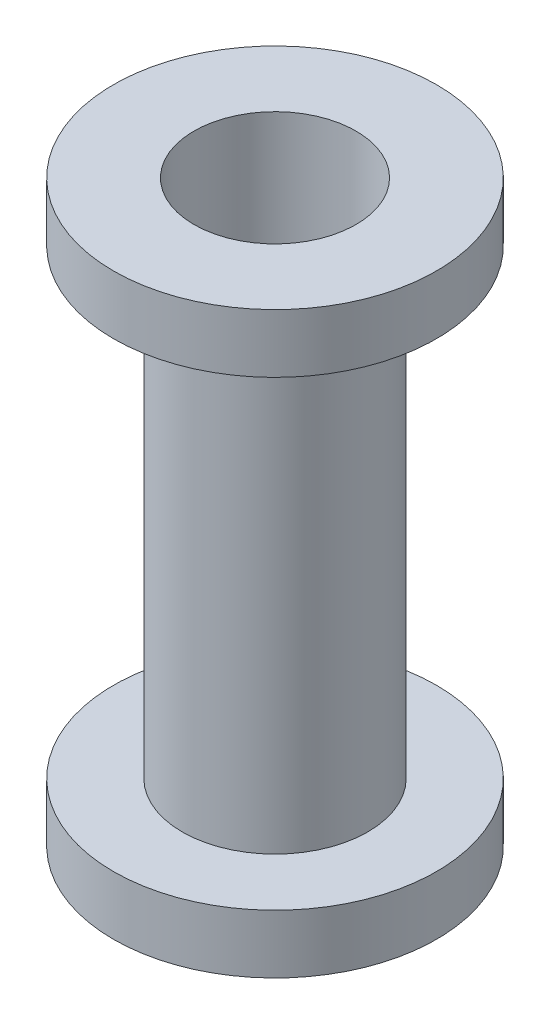
SolidWorks part; units mm, degrees
ref_plane "Front Plane" through (0, 0, 0) normal (0, 0, 1) x (1, 0, 0)
ref_plane "Top Plane" through (0, 0, 0) normal (0, 1, 0) x (1, 0, 0)
ref_plane "Right Plane" through (0, 0, 0) normal (1, 0, 0) x (0, 0, -1)
sketch "Sketch1" plane through (0, 0, 0) normal (0, 1, 0) x (1, 0, 0)
  circle A0 centre (0, 0) radius 17.526
  circle A1 centre (0, 0) radius 20.066
  dimension "D1" = 35.052
  dimension "D2" = 2.54
extrude "Extrude1" add sketch "Sketch1" along normal blind 125.222
sketch "Sketch2" plane through (0, 125.222, 0) normal (0, 1, 0) x (1, 0, 0)
  circle A0 centre (0, 0) radius 17.526
  circle A1 centre (0, 0) radius 34.925
  dimension "D1" = 69.85
extrude "Extrude2" add sketch "Sketch2" against normal blind 12.7
sketch "Sketch3" plane through (0, 0, 0) normal (0, -1, 0) x (1, 0, 0)
  circle A0 centre (0, 0) radius 17.526
  circle A1 centre (0, 0) radius 34.925
extrude "Extrude3" add sketch "Sketch3" against normal blind 12.7
